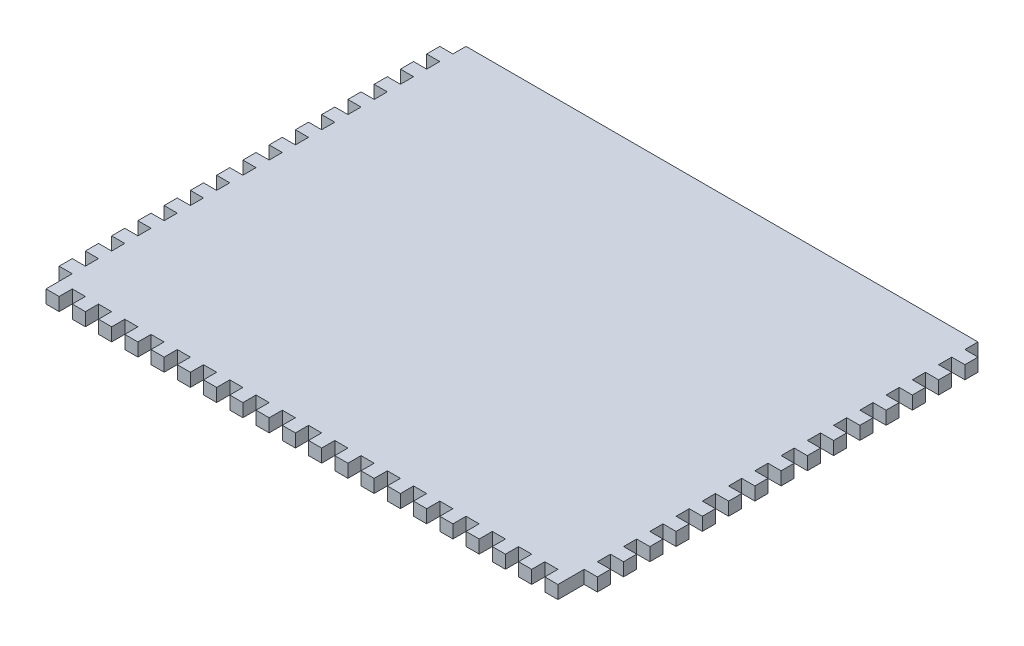
SolidWorks part; units mm, degrees
ref_plane "Front Plane" through (0, 0, 0) normal (0, 0, 1) x (1, 0, 0)
ref_plane "Top Plane" through (0, 0, 0) normal (0, 1, 0) x (1, 0, 0)
ref_plane "Right Plane" through (0, 0, 0) normal (1, 0, 0) x (0, 0, -1)
sketch "Sketch1" plane through (0, 0, 0) normal (0, 1, 0) x (1, 0, 0)
  line L1 (-130.175, -101.6) -> (130.175, -101.6)
  line L2 (-130.175, -101.6) -> (-130.175, 101.6)
  line L3 (-130.175, 101.6) -> (130.175, 101.6)
  line L4 (130.175, -101.6) -> (130.175, 101.6)
  line L5 (-130.175, -101.6) -> (130.175, 101.6) construction
  line L6 (-130.175, 101.6) -> (130.175, -101.6) construction
  point P0 (0, 0)
  dimension "D1" = 260.35
  dimension "D2" = 203.2
extrude "Boss-Extrude1" add sketch "Sketch1" along normal blind 6.35
sketch "Sketch2" plane through (0, 6.35, 0) normal (0, 1, 0) x (1, 0, 0)
  line L1 (130.175, -101.6) -> (123.825, -101.6)
  line L2 (130.175, -101.6) -> (130.175, -95.25)
  line L3 (130.175, -95.25) -> (123.825, -95.25)
  line L4 (123.825, -101.6) -> (123.825, -95.25)
  dimension "D1" = 6.35
  dimension "D2" = 6.35
extrude "Cut-Extrude1" cut sketch "Sketch2" against normal through all
pattern_linear "LPattern1" count 21 spacing 12.7 along (-1, 0, 0) of "Cut-Extrude1"
sketch "Sketch3" plane through (0, 6.35, 0) normal (0, 1, 0) x (1, 0, 0)
  line L1 (130.175, -95.25) -> (123.825, -95.25)
  line L2 (130.175, -95.25) -> (130.175, -88.9)
  line L3 (130.175, -88.9) -> (123.825, -88.9)
  line L4 (123.825, -95.25) -> (123.825, -88.9)
  dimension "D1" = 6.35
  dimension "D2" = 6.35
extrude "Cut-Extrude2" cut sketch "Sketch3" against normal through all
pattern_linear "LPattern2" count 16 spacing 12.7 along (0, 0, -1) of "Cut-Extrude2"
mirror "Mirror1" about plane through (0, 0, 0) normal (1, 0, 0) of "LPattern2", "Cut-Extrude2"
